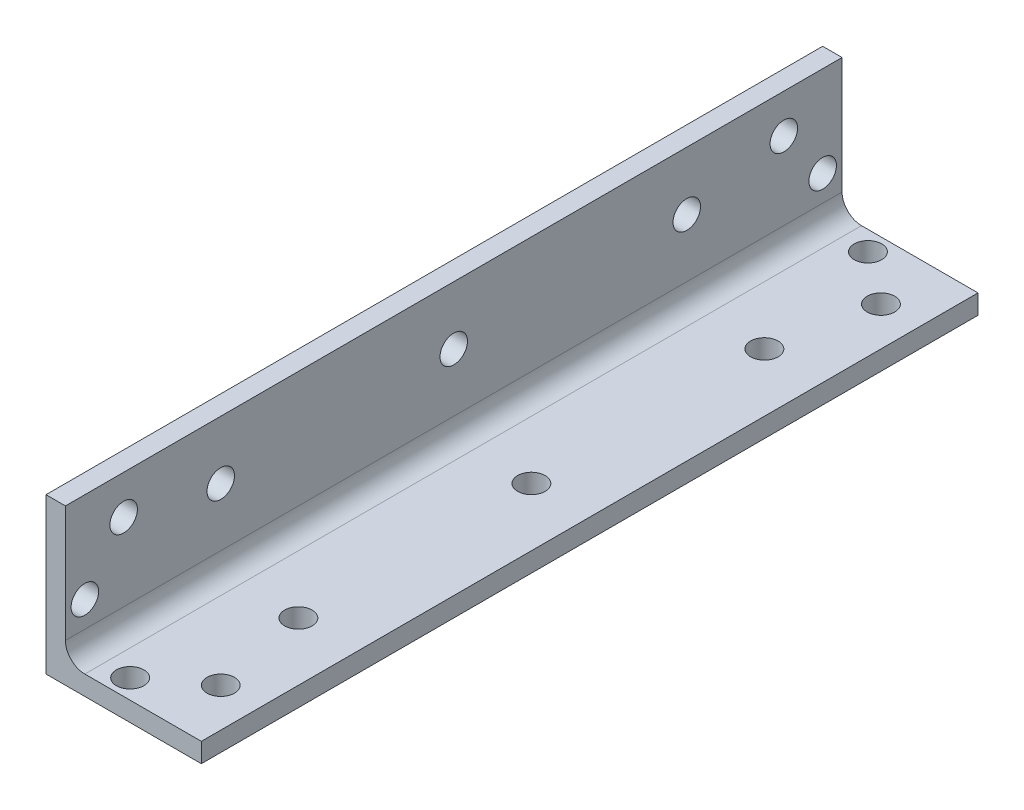
SolidWorks part; units mm, degrees
ref_plane "Front Plane" through (0, 0, 0) normal (0, 0, 1) x (1, 0, 0)
ref_plane "Top Plane" through (0, 0, 0) normal (0, 1, 0) x (1, 0, 0)
ref_plane "Right Plane" through (0, 0, 0) normal (1, 0, 0) x (0, 0, -1)
sketch "Sketch1" plane through (0, 0, 0) normal (0, 0, 1) x (1, 0, 0)
  line L0 (0, 25.4) -> (0, 0)
  line L1 (0, 0) -> (25.4, 0)
  line L2 (25.4, 0) -> (25.4, 3.175)
  line L3 (25.4, 3.175) -> (3.175, 3.175)
  line L4 (3.175, 3.175) -> (3.175, 25.4)
  line L5 (3.175, 25.4) -> (0, 25.4)
  dimension "D1" = 3.175
  dimension "D2" = 25.4
extrude "Boss-Extrude1" add sketch "Sketch1" along normal mid plane 127
fillet "Fillet1" radius 3.175 1 edges at (3.175, 3.175, 0)
sketch "Sketch2" plane through (0, 0, 0) normal (0, -1, 0) x (1, 0, 0)
  line L0 (0, -63.5) -> (25.4, -63.5) construction
  line L1 (25.4, 63.5) -> (25.4, -63.5) construction
  line L2 (0, 0) -> (25.4, 0) construction
  line L3 (0, 63.5) -> (0, -63.5) construction
  line L4 (22.225, 76.2) -> (-3.175, 76.2) construction
  line L5 (15.87, 38.1) -> (15.87, 76.2) construction
  line L6 (15.87, -38.1) -> (15.87, -76.2) construction
  line L7 (-3.175, -76.2) -> (22.225, -76.2) construction
  circle A2 centre (19.05, -53.975) radius 2.25
  circle A3 centre (10.5833, -60.325) radius 2.25
  circle A4 centre (10.5833, 60.325) radius 2.25
  circle A5 centre (19.05, 53.975) radius 2.25
  circle A6 centre (15.87, 38.1) radius 2.25
  circle A7 centre (15.87, 0) radius 2.25
  circle A8 centre (15.87, -38.1) radius 2.25
  dimension "D1" = 3.175
  dimension "D5" = 4.5
  dimension "D6" = 9.53
  dimension "D2" = 9.525
  dimension "D3" = 14.8167
  dimension "D4" = 6.35
  dimension "D7" = 3
  dimension "D8" = 38.1
extrude "Cut-Extrude1" cut sketch "Sketch2" against normal through all
ref_plane "Plane1" through (0, 0, 0) normal (0.7071, -0.7071, 0) x (0, 0, -1)
mirror "Mirror1" about plane through (0, 0, 0) normal (0.7071, -0.7071, 0) of "Cut-Extrude1"
